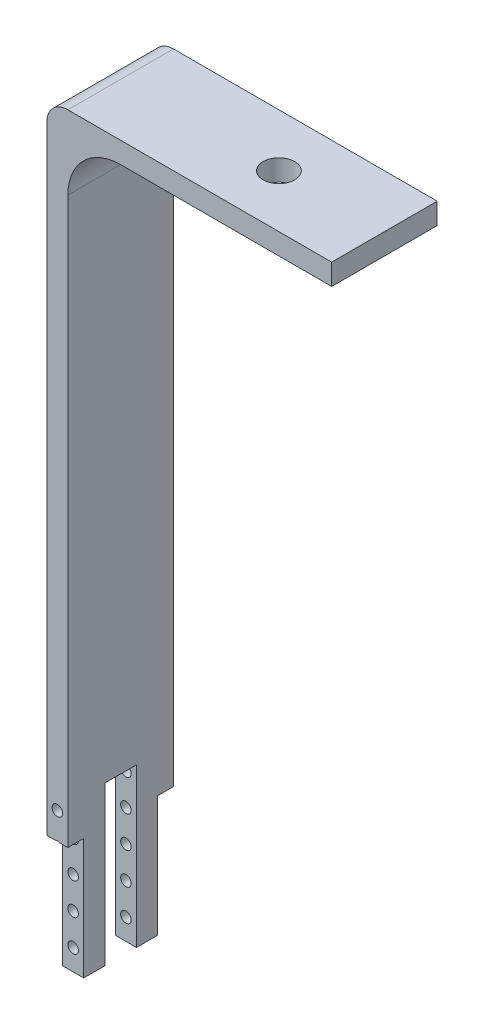
SolidWorks part; units mm, degrees
ref_plane "Ön Düzlem" through (0, 0, 0) normal (0, 0, 1) x (1, 0, 0)
ref_plane "Üst Düzlem" through (0, 0, 0) normal (0, 1, 0) x (1, 0, 0)
ref_plane "Sağ Düzlem" through (0, 0, 0) normal (1, 0, 0) x (0, 0, -1)
sketch "Çizim1" plane through (0, 0, 0) normal (0, 0, 1) x (1, 0, 0)
  line L0 (0, 38.4038) -> (0, -31.5962) construction
  line L1 (-4.7988, 38.4038) -> (-29.7988, 38.4038)
  line L2 (-29.7988, 38.4038) -> (-29.7988, -31.5962)
  line L3 (-4.7988, 40.4038) -> (-31.7988, 40.4038)
  line L4 (-31.7988, 40.4038) -> (-31.7988, -31.5962)
  line L5 (-31.7988, -31.5962) -> (-29.7988, -31.5962)
  line L6 (-4.7988, 40.4038) -> (-4.7988, 38.4038)
  dimension "D1" = 70
  dimension "D2" = 25
  dimension "D3" = 2
extrude "Yükseklik-Ekstrüzyon1" add sketch "Çizim1" along normal blind 10
sketch "Çizim2" plane through (-29.7988, 0, 0) normal (1, 0, 0) x (0, 0, -1)
  line L0 (-5, -31.5962) -> (-5, -16.5962) construction
  line L1 (-10, -31.5962) -> (0, -31.5962) construction
  line L2 (-8.5, -31.5962) -> (-8.5, -20.1415)
  line L3 (-8.5, -20.1415) -> (-10, -20.1415)
  line L4 (-10, -31.5962) -> (-10, 38.4038) construction
  line L5 (-1.5, -20.1415) -> (0, -20.1415)
  line L6 (0, -31.5962) -> (0, 38.4038) construction
  line L7 (0, -20.1415) -> (0, -31.5962)
  line L8 (0, -31.5962) -> (-1.5, -31.5962)
  line L9 (-1.5, -31.5962) -> (-1.5, -20.1415)
  line L10 (-10, -20.1415) -> (-10, -31.5962)
  line L11 (-10, -31.5962) -> (-8.5, -31.5962)
  line L13 (-6.5, -16.5962) -> (-3.5, -16.5962)
  line L14 (-6.5, -16.5962) -> (-6.5, -31.5962)
  line L15 (-6.5, -31.5962) -> (-3.5, -31.5962)
  line L16 (-3.5, -16.5962) -> (-3.5, -31.5962)
  line L17 (-6.5, -16.5962) -> (-3.5, -31.5962) construction
  line L18 (-6.5, -31.5962) -> (-3.5, -16.5962) construction
  point P6 (-5, -24.0962)
  dimension "D1" = 15
  dimension "D2" = 1.5
  dimension "D3" = 1.5
  dimension "D4" = 3
extrude "Kes-Ekstrüzyon1" cut sketch "Çizim2" against normal blind 10
sketch "Çizim3" plane through (0, 0, 8.5) normal (0, 0, 1) x (1, 0, 0)
  line L0 (-31.7988, -31.5962) -> (-29.7988, -31.5962) construction
  line L1 (-29.7988, -31.5962) -> (-29.7988, -20.1415) construction
  circle A0 centre (-30.7988, -29.5962) radius 0.5
  circle A1 centre (-30.7988, -26.5962) radius 0.5
  circle A2 centre (-30.7988, -23.5962) radius 0.5
  circle A3 centre (-30.7988, -20.5962) radius 0.5
  circle A4 centre (-30.7988, -17.5962) radius 0.5
  dimension "D1" = 1
  dimension "D2" = 2
  dimension "D3" = 1
  dimension "D4" = 5
extrude "Kes-Ekstrüzyon2" cut sketch "Çizim3" against normal mid plane 44
sketch "Çizim4" plane through (0, 40.4038, 0) normal (0, 1, 0) x (1, 0, 0)
  line L0 (-4.7988, -10) -> (-4.7988, 0) construction
  circle A0 centre (-14.7988, -5) radius 1.5
  dimension "D1" = 3
  dimension "D2" = 10
extrude "Kes-Ekstrüzyon3" cut sketch "Çizim4" against normal blind 44
fillet "Radyus1" radius 5 1 edges at (-29.7988, 38.4038, 5)
fillet "Radyus2" radius 2 1 edges at (-31.7988, 40.4038, 5)
